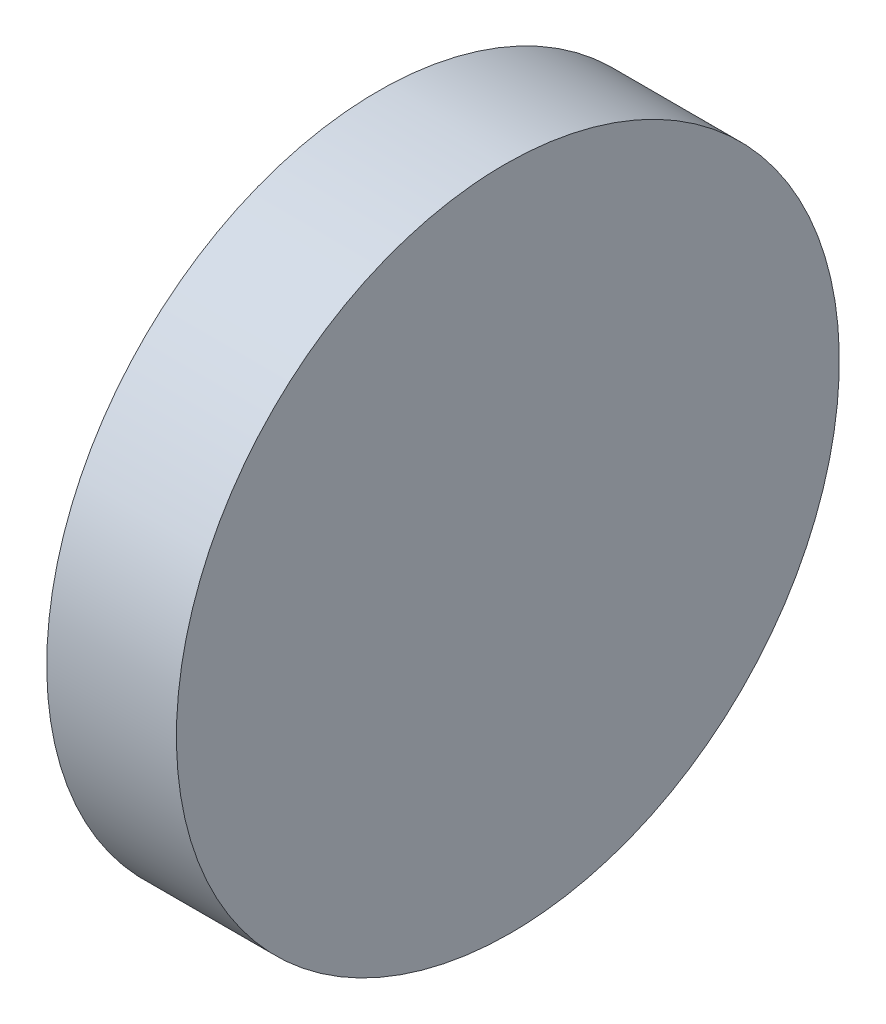
SolidWorks part; units mm, degrees
ref_plane "前视基准面" through (0, 0, 0) normal (0, 0, 1) x (1, 0, 0)
ref_plane "上视基准面" through (0, 0, 0) normal (0, 1, 0) x (1, 0, 0)
ref_plane "右视基准面" through (0, 0, 0) normal (1, 0, 0) x (0, 0, -1)
sketch "草图1" plane through (0, 0, 0) normal (0, 0, 1) x (1, 0, 0)
  line L0 (15.2768, 0) -> (-15.2768, 0) construction
  line L1 (0, 25) -> (0, -25)
  line L2 (0, -25) -> (10, -25)
  line L3 (10, -25) -> (9.5637, 25)
  line L4 (0, 25) -> (9.5637, 25)
  point P5 (0, 0)
  dimension "D1" = 10
  dimension "D2" = 50
  dimension "D3" = 0.5
extrude "凸台-拉伸1" add sketch "草图1" along normal blind 50 contours L1 L2 L3 L4
sketch "草图2" plane through (0, 0, 0) normal (-1, 0, 0) x (0, 0, 1)
  line L4 (0, 25) -> (0, -25)
  line L5 (0, -25) -> (50, -25)
  line L6 (50, -25) -> (50, 25)
  line L7 (50, 25) -> (0, 25)
  line L8 (0, 25) -> (0, -25)
  line L9 (0, -25) -> (50, -25)
  line L10 (50, -25) -> (50, 25)
  line L11 (50, 25) -> (0, 25)
  circle A0 centre (25, 0) radius 25
  point P7 (25, 25)
  line M1 (0, 25) -> (0, -25)
  line M2 (0, -25) -> (50, -25)
  line M3 (50, -25) -> (50, 25)
  line M4 (50, 25) -> (0, 25)
  dimension "D2" = 50
  dimension "D1" = 0
extrude "切除-拉伸1" cut sketch "草图2" against normal blind 10 contours A0 L8 M2 | A0 L9 M3 | A0 L10 M4 | A0 L11 M1
